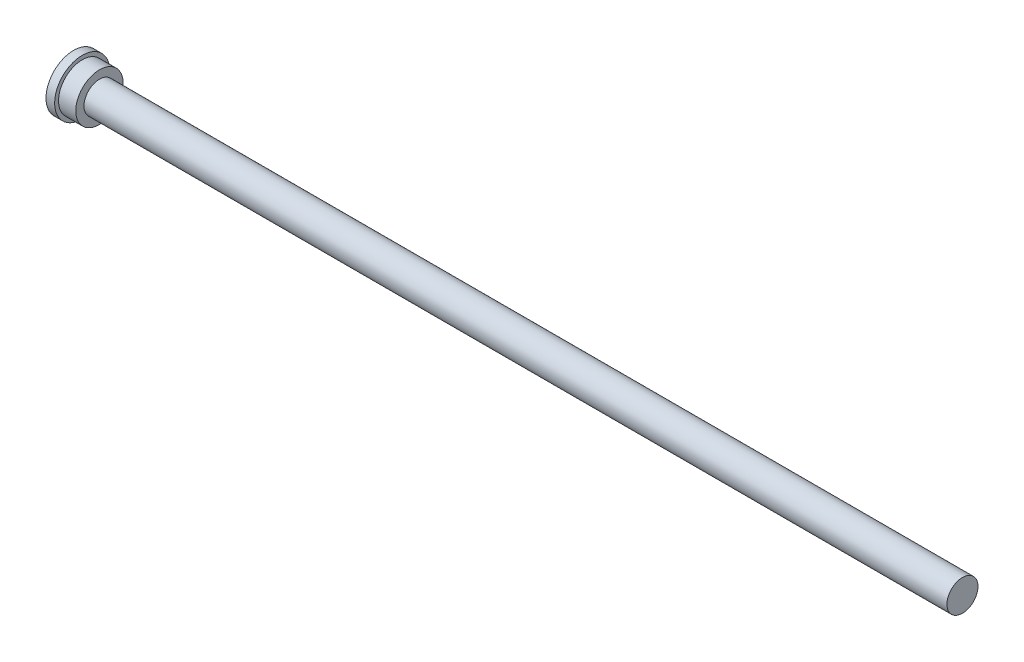
SolidWorks part; units mm, degrees
ref_plane "Front Plane" through (0, 0, 0) normal (0, 0, 1) x (1, 0, 0)
ref_plane "Top Plane" through (0, 0, 0) normal (0, 1, 0) x (1, 0, 0)
ref_plane "Right Plane" through (0, 0, 0) normal (1, 0, 0) x (0, 0, -1)
sketch "Sketch1" plane through (0, 0, 0) normal (1, 0, 0) x (0, 0, -1)
  circle A0 centre (0, 0) radius 34.925
  dimension "D1" = 69.85
extrude "Boss-Extrude1" add sketch "Sketch1" along normal blind 25.4
sketch "Sketch2" plane through (25.4, 0, 0) normal (1, 0, 0) x (0, 0, -1)
  circle A0 centre (0, 0) radius 22.86
  dimension "D1" = 45.72
extrude "Boss-Extrude2" add sketch "Sketch2" along normal blind 1270
sketch "Sketch3" plane through (0, 0, 0) normal (-1, 0, 0) x (0, 0, 1)
  circle A0 centre (0, 0) radius 40.64
  dimension "D1" = 81.28
extrude "Boss-Extrude3" add sketch "Sketch3" along normal blind 12.7
